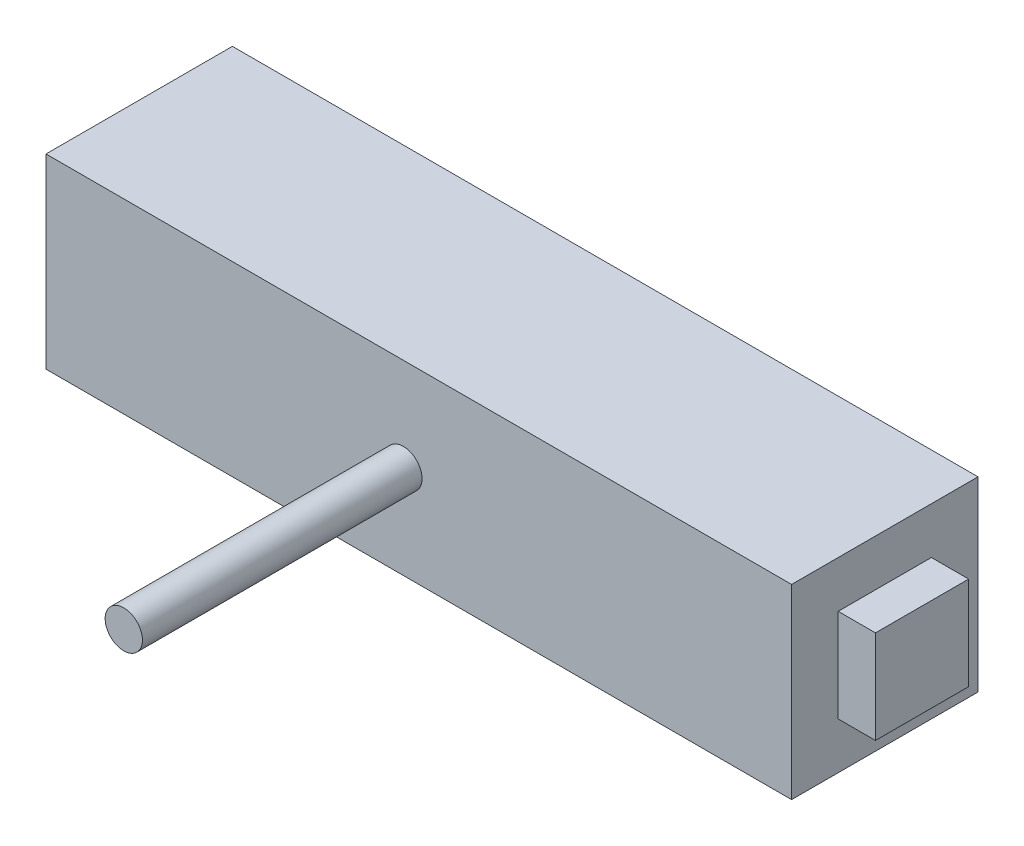
SolidWorks part; units mm, degrees
ref_plane "Front Plane" through (0, 0, 0) normal (0, 0, 1) x (1, 0, 0)
ref_plane "Top Plane" through (0, 0, 0) normal (0, 1, 0) x (1, 0, 0)
ref_plane "Right Plane" through (0, 0, 0) normal (1, 0, 0) x (0, 0, -1)
sketch "Sketch1" plane through (0, 0, 0) normal (0, 1, 0) x (1, 0, 0)
  line L1 (-50.8, 12.7) -> (50.8, 12.7)
  line L2 (-50.8, 12.7) -> (-50.8, -12.7)
  line L3 (-50.8, -12.7) -> (50.8, -12.7)
  line L4 (50.8, 12.7) -> (50.8, -12.7)
  line L5 (-50.8, 12.7) -> (50.8, -12.7) construction
  line L6 (-50.8, -12.7) -> (50.8, 12.7) construction
  point P0 (0, 0)
  dimension "D1" = 101.6
  dimension "D2" = 25.4
extrude "Boss-Extrude1" add sketch "Sketch1" along normal blind 25.4
sketch "Sketch2" plane through (50.8, 0, 0) normal (1, 0, 0) x (0, 0, -1)
  line L1 (-6.35, 19.05) -> (6.35, 19.05)
  line L2 (-6.35, 19.05) -> (-6.35, 6.35)
  line L3 (-6.35, 6.35) -> (6.35, 6.35)
  line L4 (6.35, 19.05) -> (6.35, 6.35)
  line L5 (-6.35, 19.05) -> (6.35, 6.35) construction
  line L6 (-6.35, 6.35) -> (6.35, 19.05) construction
  point P0 (0, 12.7)
  dimension "D1" = 6.35
  dimension "D2" = 12.7
  dimension "D3" = 6.35
  dimension "D4" = 12.7
extrude "Boss-Extrude2" add sketch "Sketch2" along normal blind 5.08
sketch "Sketch6" plane through (0, 0, 12.7) normal (0, 0, 1) x (1, 0, 0)
  circle A0 centre (-2.1011, 12.7) radius 2.54
  point P2 (0, 0)
  dimension "D1" = 5.08
  dimension "D2" = 52.9011
  dimension "D3" = 52.9011
  dimension "D4" = 12.7
extrude "Boss-Extrude4" add sketch "Sketch6" along normal blind 38.1
